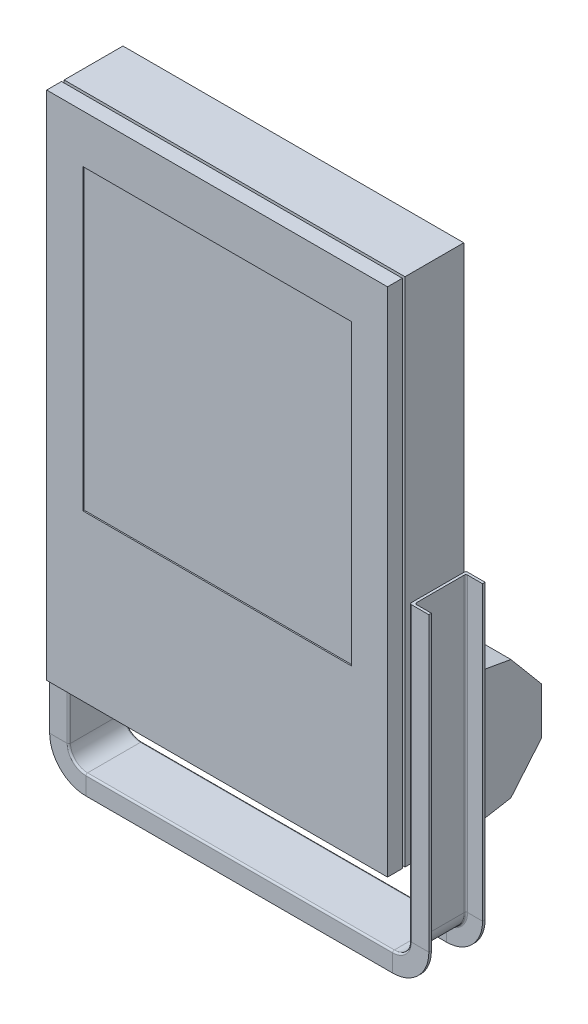
SolidWorks part; units mm, degrees
ref_plane "Front Plane" through (0, 0, 0) normal (0, 0, 1) x (1, 0, 0)
ref_plane "Top Plane" through (0, 0, 0) normal (0, 1, 0) x (1, 0, 0)
ref_plane "Right Plane" through (0, 0, 0) normal (1, 0, 0) x (0, 0, -1)
sketch "Sketch1" plane through (0, 0, 0) normal (0, 0, 1) x (1, 0, 0)
  line L1 (-200, -300) -> (200, -300)
  line L2 (-200, -300) -> (-200, 300)
  line L3 (-200, 300) -> (200, 300)
  line L4 (200, -300) -> (200, 300)
  line L5 (-200, -300) -> (200, 300) construction
  line L6 (-200, 300) -> (200, -300) construction
  point P0 (0, 0)
  dimension "D1" = 600
  dimension "D2" = 400
extrude "Boss-Extrude1" add sketch "Sketch1" along normal blind 89.5
sketch "Sketch2" plane through (0, 0, 89.5) normal (0, 0, 1) x (1, 0, 0)
  line L0 (-200, 300) -> (-200, -300) construction
  line L1 (-157.5, 243.5) -> (157.5, 243.5)
  line L2 (-157.5, 243.5) -> (-157.5, -106.5)
  line L3 (-157.5, -106.5) -> (157.5, -106.5)
  line L4 (157.5, 243.5) -> (157.5, -106.5)
  line L5 (200, 300) -> (-200, 300) construction
  dimension "D1" = 42.5
  dimension "D2" = 56.5
  dimension "D3" = 315
  dimension "D4" = 350
extrude "Cut-Extrude1" cut sketch "Sketch2" against normal blind 1.5
sketch "Sketch3" plane through (0, -300, 0) normal (0, -1, 0) x (1, 0, 0)
  line L0 (-200, 89.5) -> (-200, 0) construction
  line L1 (-200, 72.1) -> (-181.5, 72.1)
  line L2 (-200, 72.1) -> (-200, 69)
  line L3 (-200, 69) -> (-181.5, 69)
  line L4 (-181.5, 72.1) -> (-181.5, 69)
  line L5 (-200, 0) -> (200, 0) construction
  dimension "D1" = 3.1
  dimension "D2" = 18.5
  dimension "D3" = 69
extrude "Cut-Extrude2" cut sketch "Sketch3" against normal up to next (600 mm away)
mirror "Mirror1" about plane through (0, 0, 0) normal (1, 0, 0) of "Cut-Extrude2"
sketch "Sketch5" plane through (181.5, 0, 0) normal (1, 0, 0) x (0, 0, -1)
  line L0 (-69, 300) -> (-69, -300) construction
  line L1 (-72.1, -300) -> (-69, -300)
  line L2 (-72.1, -300) -> (-72.1, -281.5)
  line L3 (-72.1, -281.5) -> (-69, -281.5)
  line L4 (-69, -300) -> (-69, -281.5)
  dimension "D1" = 18.5
extrude "Cut-Extrude3" cut sketch "Sketch5" against normal up to next (363 mm away)
mirror "Mirror2" about plane through (0, 0, 0) normal (0, 1, 0) of "Cut-Extrude3"
ref_plane "Plane1" through (0, -35, 0) normal (0, 1, 0) x (1, 0, 0)
sketch "Sketch10" plane through (0, -35, 0) normal (0, 1, 0) x (1, 0, 0)
  line L0 (-231.2479, -30.5) -> (241.4182, -30.5) construction
  line L2 (-200, 0.5) -> (-200, -61.5)
  line L3 (-200, -69) -> (-200, 0) construction
  line L4 (-202, 2.5) -> (-222.5, 2.5)
  line L5 (-202, -63.5) -> (-222.5, -63.5)
  line L6 (-222.5, 2.5) -> (-222.5, -0.5)
  line L7 (-222.5, -0.5) -> (-205, -0.5)
  line L8 (-203, -2.5) -> (-203, -58.5)
  line L9 (-222.5, -63.5) -> (-222.5, -60.5)
  line L10 (-222.5, -60.5) -> (-205, -60.5)
  line L11 (-181.5, -69) -> (181.5, -69) construction
  arc A0 (-200, -61.5) -> (-202, -63.5) centre (-202, -61.5) cw
  arc A1 (-203, -58.5) -> (-205, -60.5) centre (-205, -58.5) cw
  arc A2 (-203, -2.5) -> (-205, -0.5) centre (-205, -2.5) ccw
  arc A3 (-200, 0.5) -> (-202, 2.5) centre (-202, 0.5) ccw
  point P16 (-200, -63.5)
  point P23 (-200, 2.5)
  dimension "D9" = 2
  dimension "D1" = 38.5
  dimension "D2" = 66
  dimension "D3" = 33
  dimension "D4" = 22.5
  dimension "D5" = 22.5
  dimension "D6" = 3
  dimension "D7" = 3
  dimension "D8" = 3
sketch "Sketch11" plane through (0, 0, 0) normal (0, 0, 1) x (1, 0, 0)
  line L0 (-200, -35) -> (-200, -378)
  line L1 (-180, -398) -> (180, -398)
  line L3 (-231.2479, -35) -> (241.4182, -35) construction
  line L4 (200, -300) -> (200, 300) construction
  line L5 (200, -35) -> (200, -378)
  arc A0 (200, -378) -> (180, -398) centre (180, -378) cw
  arc A1 (-180, -398) -> (-200, -378) centre (-180, -378) cw
  point P13 (-200, -398)
  dimension "D2" = 20
  dimension "D1" = 363
sketch "Sketch12" plane through (-200, 0, 0) normal (-1, 0, 0) x (0, 0, 1)
  line L0 (69, 300) -> (69, -300) construction
  line L1 (69, -221.5) -> (-96.979, -221.5) construction
  line L2 (69, -143) -> (0, -143)
  line L3 (69, -143) -> (-62.0337, -143) construction
  line L4 (69, -221.5) -> (-62.0337, -221.5) construction
  line L8 (-55.2803, -151.1459) -> (-91, -193.715)
  line L9 (-91, -193.715) -> (-91, -249.285)
  line L10 (-91, -249.285) -> (-55.2803, -291.8541)
  line L12 (-55.2803, -291.8541) -> (-9.0825, -300)
  line L13 (0, -300) -> (-9.0825, -300)
  line L14 (-55.2803, -151.1459) -> (0, -141.3985)
  line L15 (0, 300) -> (0, -300) construction
  line L16 (0, -141.3985) -> (0, -300)
  point P15 (12.6485, -139.1682)
  dimension "D3" = 160
  dimension "D4" = 140
  dimension "D5" = 140
  dimension "D6" = 140
  dimension "D7" = 55.57
  dimension "D8" = 55.57
  dimension "D9" = 55.57
  dimension "D10" = 140
  dimension "D1" = 157
  dimension "D2" = 78.5
extrude "Boss-Extrude2" add sketch "Sketch12" against normal up to surface (400 mm away) up to face at (200, 0, 34.5)
sweep "Sweep1" add profiles "Sketch10" path "Sketch11"
